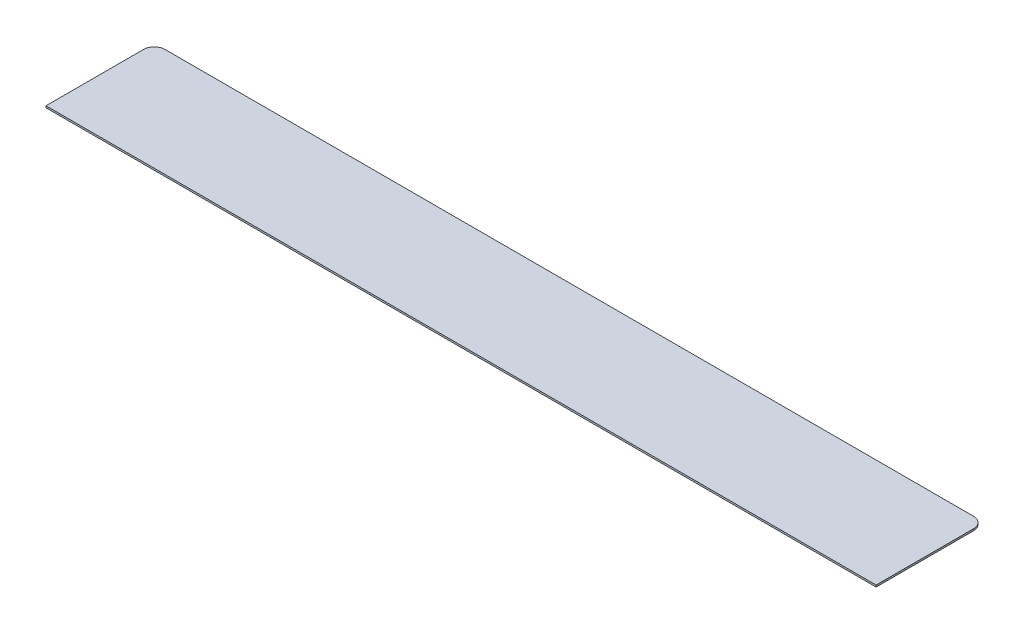
SolidWorks part; units mm, degrees
ref_plane "Front Plane" through (0, 0, 0) normal (0, 0, 1) x (1, 0, 0)
ref_plane "Top Plane" through (0, 0, 0) normal (0, 1, 0) x (1, 0, 0)
ref_plane "Right Plane" through (0, 0, 0) normal (1, 0, 0) x (0, 0, -1)
sketch "Sketch1" plane through (0, 0, 0) normal (0, 1, 0) x (1, 0, 0)
  line L1 (-115, 15) -> (115, 15)
  line L2 (-115, 15) -> (-115, -15)
  line L3 (-115, -15) -> (115, -15)
  line L4 (115, 15) -> (115, -15)
  line L5 (-115, 15) -> (115, -15) construction
  line L6 (-115, -15) -> (115, 15) construction
  point P0 (0, 0)
  dimension "D1" = 30
  dimension "D2" = 230
extrude "Boss-Extrude1" add sketch "Sketch1" along normal blind 0.5
fillet "Fillet1" radius 3 2 edges at (115, 0.25, -15) (-115, 0.25, -15)
